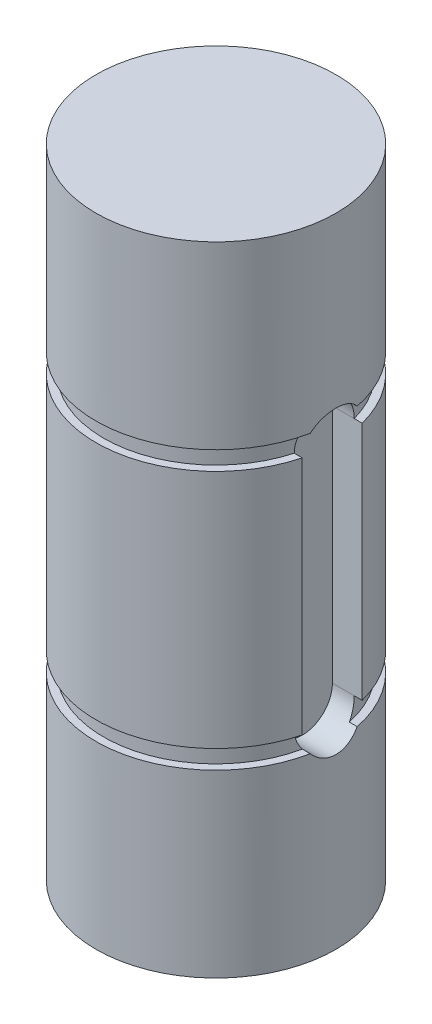
SolidWorks part; units mm, degrees
material "AISI 1020"
ref_plane "Front Plane" through (0, 0, 0) normal (0, 0, 1) x (1, 0, 0)
ref_plane "Top Plane" through (0, 0, 0) normal (0, 1, 0) x (1, 0, 0)
ref_plane "Right Plane" through (0, 0, 0) normal (1, 0, 0) x (0, 0, -1)
sketch "Sketch1" plane through (0, 0, 0) normal (0, 1, 0) x (1, 0, 0)
  circle A0 centre (0, 0) radius 6.35
extrude "Boss-Extrude1" add sketch "Sketch1" along normal blind 33.7312 contours A0
sketch "Sketch2" plane through (0, 0, 0) normal (1, 0, 0) x (0, 0, -1)
  line L0 (6.35, 33.7312) -> (-6.35, 33.7312) construction
  line L1 (-26.692, 24.2062) -> (-5.9436, 24.2062)
  line L2 (-26.692, 24.2062) -> (-26.692, 23.2156)
  line L3 (-26.692, 23.2156) -> (-5.9436, 23.2156)
  line L4 (-5.9436, 24.2062) -> (-5.9436, 23.2156)
  line L5 (-6.35, 33.7312) -> (-6.35, 0) construction
  line L6 (0, 25.5171) -> (0, 18.5583) construction
  dimension "D1" = 9.525
  dimension "D2" = 0.9906
  dimension "D3" = 0.4064
revolve "Cut-Revolve1" cut sketch "Sketch2" angle 360 about L6
sketch "Sketch3" plane through (0, 0, 0) normal (1, 0, 0) x (0, 0, -1)
  line L0 (6.35, 23.2156) -> (-6.35, 23.2156) construction
  line L1 (-21.2804, 10.5156) -> (-5.9436, 10.5156)
  line L2 (-21.2804, 10.5156) -> (-21.2804, 9.525)
  line L3 (-21.2804, 9.525) -> (-5.9436, 9.525)
  line L4 (-5.9436, 10.5156) -> (-5.9436, 9.525)
  line L5 (-6.35, 23.2156) -> (-6.35, 0) construction
  line L6 (0, 15.8106) -> (0, 5.0331) construction
  dimension "D1" = 12.7
  dimension "D2" = 0.9906
  dimension "D3" = 0.4064
revolve "Cut-Revolve2" cut sketch "Sketch3" angle 360 about L6
ref_plane "Plane1" through (6.35, 0, 0) normal (1, 0, 0) x (0, 0, -1)
sketch "Sketch4" plane through (6.35, 0, 0) normal (1, 0, 0) x (0, 0, -1)
  line L0 (0, 23.2156) -> (0, 10.5156) construction
  line L1 (6.35, 23.2156) -> (-6.35, 23.2156) construction
  line L2 (-5.9436, 10.5156) -> (5.9436, 10.5156) construction
  line L3 (1.5875, 23.2156) -> (1.5875, 10.5156)
  line L4 (-1.5875, 23.2156) -> (-1.5875, 10.5156)
  arc A0 (1.5875, 23.2156) -> (-1.5875, 23.2156) centre (0, 23.2156) ccw
  arc A1 (-1.5875, 10.5156) -> (1.5875, 10.5156) centre (0, 10.5156) ccw
  point P6 (0, 16.8656)
extrude "Cut-Extrude1" cut sketch "Sketch4" against normal blind 1.778 contours L4 A1 L3 A0
